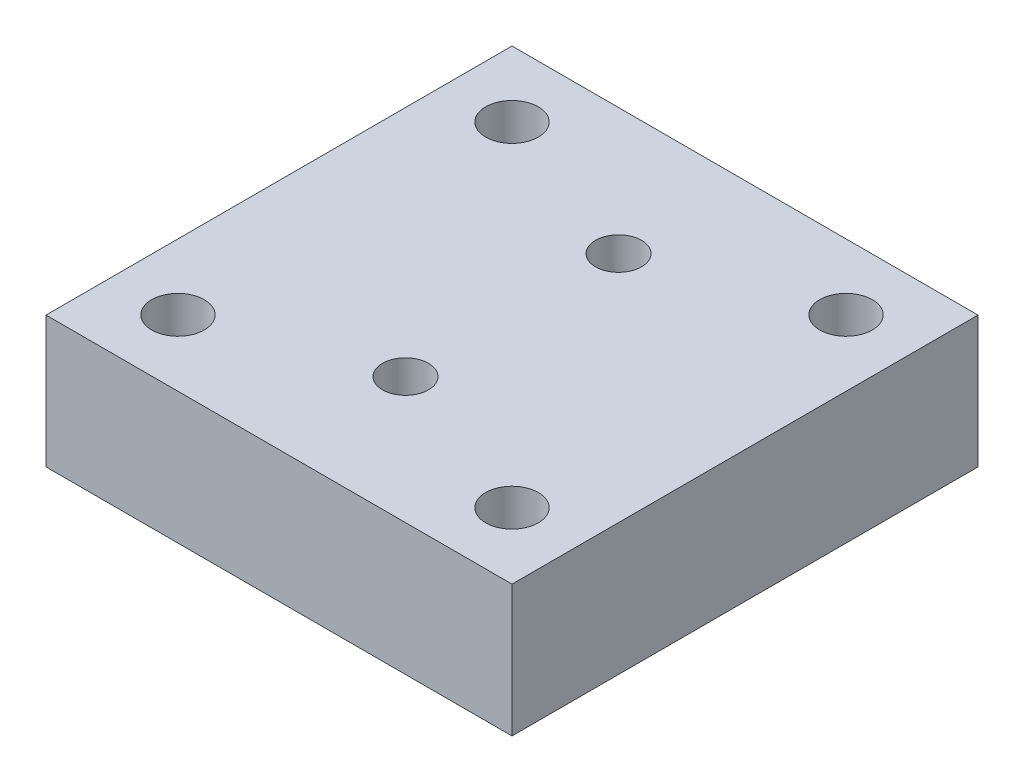
SolidWorks part; units mm, degrees
ref_plane "Front Plane" through (0, 0, 0) normal (0, 0, 1) x (1, 0, 0)
ref_plane "Top Plane" through (0, 0, 0) normal (0, 1, 0) x (1, 0, 0)
ref_plane "Right Plane" through (0, 0, 0) normal (1, 0, 0) x (0, 0, -1)
sketch "Sketch1" plane through (0, 0, 0) normal (0, 1, 0) x (1, 0, 0)
  line L1 (-45, 45) -> (45, 45)
  line L2 (-45, 45) -> (-45, -45)
  line L3 (-45, -45) -> (45, -45)
  line L4 (45, 45) -> (45, -45)
  line L5 (-45, 45) -> (45, -45) construction
  line L6 (-45, -45) -> (45, 45) construction
  point P0 (0, 0)
  dimension "D1" = 90
  dimension "D2" = 90
extrude "Boss-Extrude1" add sketch "Sketch1" along normal blind 25.4
sketch "Sketch2" plane through (0, 25.4, 0) normal (0, 1, 0) x (-1, 0, 0)
  line L0 (-45, -45) -> (45, -45) construction
  line L1 (45, -45) -> (45, 45) construction
  circle A0 centre (32.3, -32.3) radius 5.08
  dimension "D1" = 10.16
  dimension "D2" = 12.7
  dimension "D3" = 12.7
extrude "Cut-Extrude1" cut sketch "Sketch2" against normal blind 50.8 contours A0
pattern_linear "LPattern1" count 2 spacing 64.516 along (1, 0, 0) count 2 spacing 64.516 along (0, 0, 1) of "Cut-Extrude1"
sketch "Sketch4" plane through (0, 25.4, 0) normal (0, 1, 0) x (1, 0, 0)
  line L1 (-7.62, 28.194) -> (7.62, 28.194)
  line L2 (-7.62, 28.194) -> (-7.62, -28.194)
  line L3 (-7.62, -28.194) -> (7.62, -28.194)
  line L4 (7.62, 28.194) -> (7.62, -28.194)
  line L5 (-7.62, 28.194) -> (7.62, -28.194) construction
  line L6 (-7.62, -28.194) -> (7.62, 28.194) construction
  circle A0 centre (0, 20.574) radius 4.445
  circle A1 centre (0, -20.574) radius 4.445
  point P0 (0, 0)
  point P8 (0, 0)
  point P11 (0, -21.1546)
  point P14 (1.019, -3.7703)
  point P15 (-7.62, -20.7031)
  point P16 (0.2082, -21.482)
  dimension "D3" = 8.89
  dimension "D1" = 15.24
  dimension "D2" = 56.388
  dimension "D4" = 7.62
  dimension "D5" = 7.62
  dimension "D6" = 7.62
extrude "Cut-Extrude3" cut sketch "Sketch4" against normal through all contours A0 | A1
sketch "Sketch5" plane through (0, 0, 0) normal (0, -1, 0) x (1, 0, 0)
  circle A0 centre (0, -20.574) radius 8.89
  circle A1 centre (0, 20.574) radius 8.89
  dimension "D1" = 17.78
  dimension "D2" = 17.78
extrude "Cut-Extrude4" cut sketch "Sketch5" against normal blind 7.62
